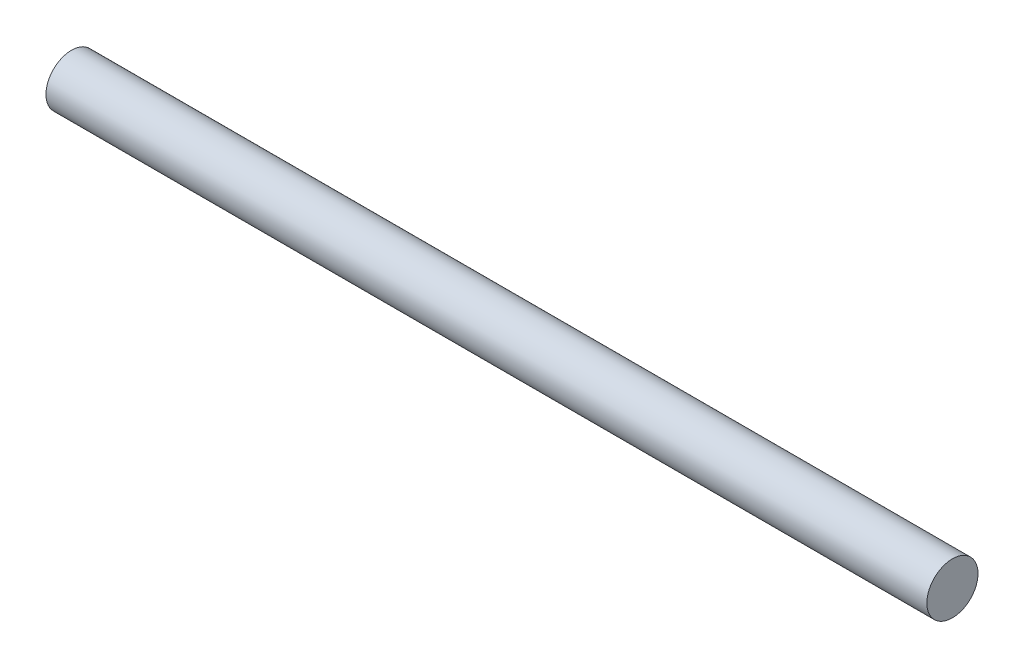
SolidWorks part; units mm, degrees
ref_plane "Plan de face" through (0, 0, 0) normal (0, 0, 1) x (1, 0, 0)
ref_plane "Plan de dessus" through (0, 0, 0) normal (0, 1, 0) x (1, 0, 0)
ref_plane "Plan de droite" through (0, 0, 0) normal (1, 0, 0) x (0, 0, -1)
sketch "Esquisse5" plane through (0, 0, 0) normal (1, 0, 0) x (0, 0, -1)
  circle A0 centre (0, 0) radius 18
extrude "Boss.-Extru.3" add sketch "Esquisse5" along normal blind 620
ref_plane "Plan2" through (10, 0, 0) normal (-1, 0, 0) x (0, 0, 1)
ref_plane "Plan4" through (610, 0, 0) normal (-1, 0, 0) x (0, 0, 1)
sketch "Esquisse6" plane through (10, 0, 0) normal (-1, 0, 0) x (0, 0, 1)
  circle A0 centre (0, 0) radius 18
sketch "Esquisse7" plane through (610, 0, 0) normal (-1, 0, 0) x (0, 0, 1)
  circle A0 centre (0, 0) radius 18
ref_plane "Plan31" through (590, 0, 0) normal (-1, 0, 0) x (0, 0, 1)
sketch "Esquisse32" plane through (590, 0, 0) normal (-1, 0, 0) x (0, 0, 1)
  circle A0 centre (0, 0) radius 18
ref_plane "Plan50" through (530, 0, 0) normal (-1, 0, 0) x (0, 0, 1)
ref_plane "Plan51" through (510, 0, 0) normal (-1, 0, 0) x (0, 0, 1)
ref_plane "Plan52" through (450, 0, 0) normal (-1, 0, 0) x (0, 0, 1)
ref_plane "Plan53" through (430, 0, 0) normal (-1, 0, 0) x (0, 0, 1)
ref_plane "Plan54" through (370, 0, 0) normal (-1, 0, 0) x (0, 0, 1)
ref_plane "Plan55" through (250, 0, 0) normal (-1, 0, 0) x (0, 0, 1)
ref_plane "Plan56" through (190, 0, 0) normal (-1, 0, 0) x (0, 0, 1)
ref_plane "Plan57" through (170, 0, 0) normal (-1, 0, 0) x (0, 0, 1)
ref_plane "Plan58" through (110, 0, 0) normal (-1, 0, 0) x (0, 0, 1)
ref_plane "Plan59" through (90, 0, 0) normal (-1, 0, 0) x (0, 0, 1)
ref_plane "Plan60" through (30, 0, 0) normal (-1, 0, 0) x (0, 0, 1)
sketch "Esquisse53" plane through (530, 0, 0) normal (-1, 0, 0) x (0, 0, 1)
  circle A0 centre (0, 0) radius 18
sketch "Esquisse54" plane through (510, 0, 0) normal (-1, 0, 0) x (0, 0, 1)
  circle A0 centre (0, 0) radius 18
sketch "Esquisse55" plane through (450, 0, 0) normal (-1, 0, 0) x (0, 0, 1)
  circle A0 centre (0, 0) radius 18
sketch "Esquisse56" plane through (430, 0, 0) normal (-1, 0, 0) x (0, 0, 1)
  circle A0 centre (0, 0) radius 18
sketch "Esquisse57" plane through (370, 0, 0) normal (-1, 0, 0) x (0, 0, 1)
  circle A0 centre (0, 0) radius 18
sketch "Esquisse58" plane through (250, 0, 0) normal (-1, 0, 0) x (0, 0, 1)
  circle A0 centre (0, 0) radius 18
sketch "Esquisse59" plane through (190, 0, 0) normal (-1, 0, 0) x (0, 0, 1)
  circle A0 centre (0, 0) radius 18
sketch "Esquisse60" plane through (170, 0, 0) normal (-1, 0, 0) x (0, 0, 1)
  circle A0 centre (0, 0) radius 18
sketch "Esquisse61" plane through (30, 0, 0) normal (-1, 0, 0) x (0, 0, 1)
  circle A0 centre (0, 0) radius 18
sketch "Esquisse62" plane through (90, 0, 0) normal (-1, 0, 0) x (0, 0, 1)
  circle A0 centre (0, 0) radius 18
